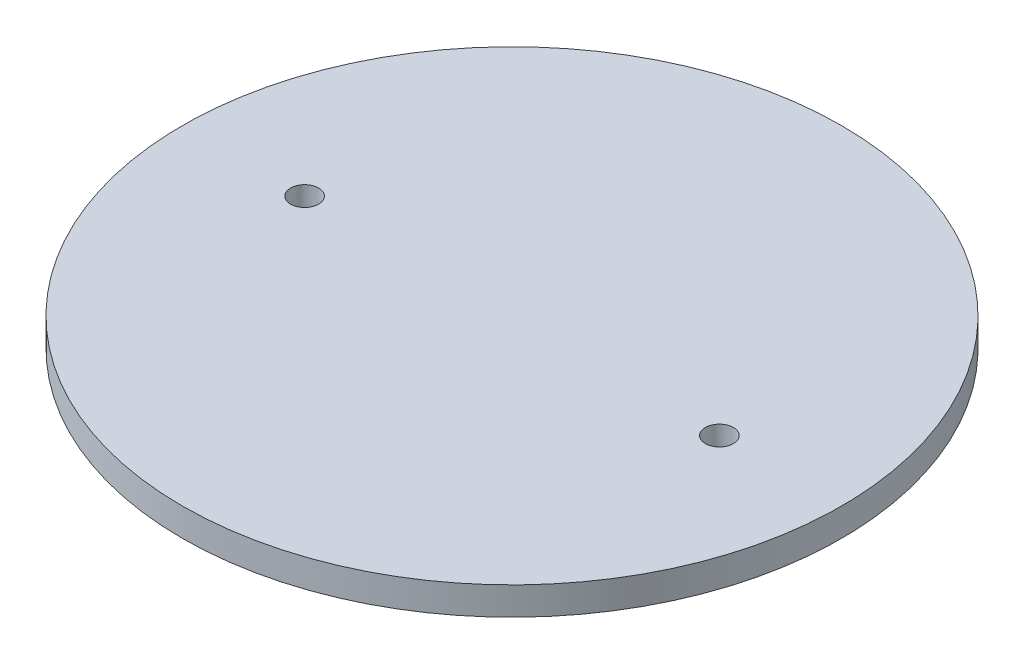
SolidWorks part; units mm, degrees
material "ABS PC"
ref_plane "前视基准面" through (0, 0, 0) normal (0, 0, 1) x (1, 0, 0)
ref_plane "上视基准面" through (0, 0, 0) normal (0, 1, 0) x (1, 0, 0)
ref_plane "右视基准面" through (0, 0, 0) normal (1, 0, 0) x (0, 0, -1)
sketch "Sketch1" plane through (0, 0, 0) normal (0, 1, 0) x (1, 0, 0)
  circle A0 centre (0, 0) radius 74.676
  dimension "D1" = 149.352
extrude "Boss-Extrude1" add sketch "Sketch1" along normal blind 6.35
sketch "Sketch2" plane through (0, 6.35, 0) normal (0, 1, 0) x (1, 0, 0)
  line L1 (-66.782, 0) -> (66.782, 0) construction
  circle A0 centre (15.3979, 33.02) radius 1.651
  circle A1 centre (0, 41.91) radius 21.4376 construction
  circle A2 centre (0, 41.91) radius 5.5626
  circle A3 centre (0, 59.69) radius 1.651
  circle A4 centre (-15.3979, 33.02) radius 1.651
  circle A5 centre (0, -59.69) radius 1.651
  circle A6 centre (-15.3979, -33.02) radius 1.651
  circle A7 centre (0, -41.91) radius 5.5626
  circle A8 centre (15.3979, -33.02) radius 1.651
  point P14 (0, 47.371)
  point P16 (0.2016, 36.7982)
  point P24 (0, 41.91)
  dimension "D1" = 42.8752
  dimension "D2" = 11.1252
  dimension "D4" = 3.302
  dimension "D3" = 17.78
  dimension "D6" = 83.82
  dimension "D7" = 41.91
  dimension "D5" = 3
sketch "Sketch3" plane through (0, 6.35, 0) normal (0, 1, 0) x (1, 0, 0)
  line L0 (-74.676, 0) -> (74.676, 0) construction
  line L1 (0, 74.676) -> (0, -74.676) construction
  circle A1 centre (-46.99, 0) radius 3.175
  circle A3 centre (46.99, 0) radius 3.175
  dimension "D1" = 6.35
  dimension "D2" = 93.98
extrude "1/4 Holes" cut sketch "Sketch3" against normal up to surface (6.35 mm away) up to face at (0, 0, 74.676)
